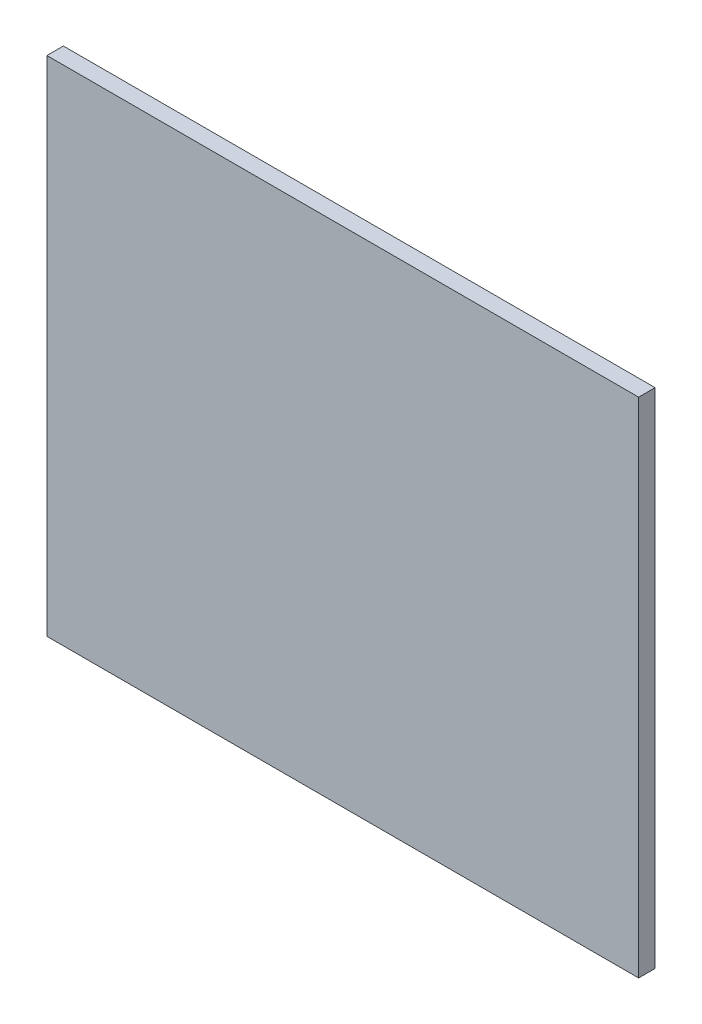
SolidWorks part; units mm, degrees
ref_plane "Front Plane" through (0, 0, 0) normal (0, 0, 1) x (1, 0, 0)
ref_plane "Top Plane" through (0, 0, 0) normal (0, 1, 0) x (1, 0, 0)
ref_plane "Right Plane" through (0, 0, 0) normal (1, 0, 0) x (0, 0, -1)
sketch "Sketch1" plane through (0, 0, 0) normal (0, 0, 1) x (1, 0, 0)
  line L1 (323.5, -275) -> (-323.5, -275)
  line L2 (323.5, -275) -> (323.5, 275)
  line L3 (323.5, 275) -> (-323.5, 275)
  line L4 (-323.5, -275) -> (-323.5, 275)
  line L5 (323.5, -275) -> (-323.5, 275) construction
  line L6 (323.5, 275) -> (-323.5, -275) construction
  point P0 (0, 0)
  dimension "D1" = 550
  dimension "D2" = 647
extrude "Boss-Extrude1" add sketch "Sketch1" along normal blind 18
equation "\"H_DSP\"=18"
equation "\"D1@Boss-Extrude1\"=\"H_DSP\""
